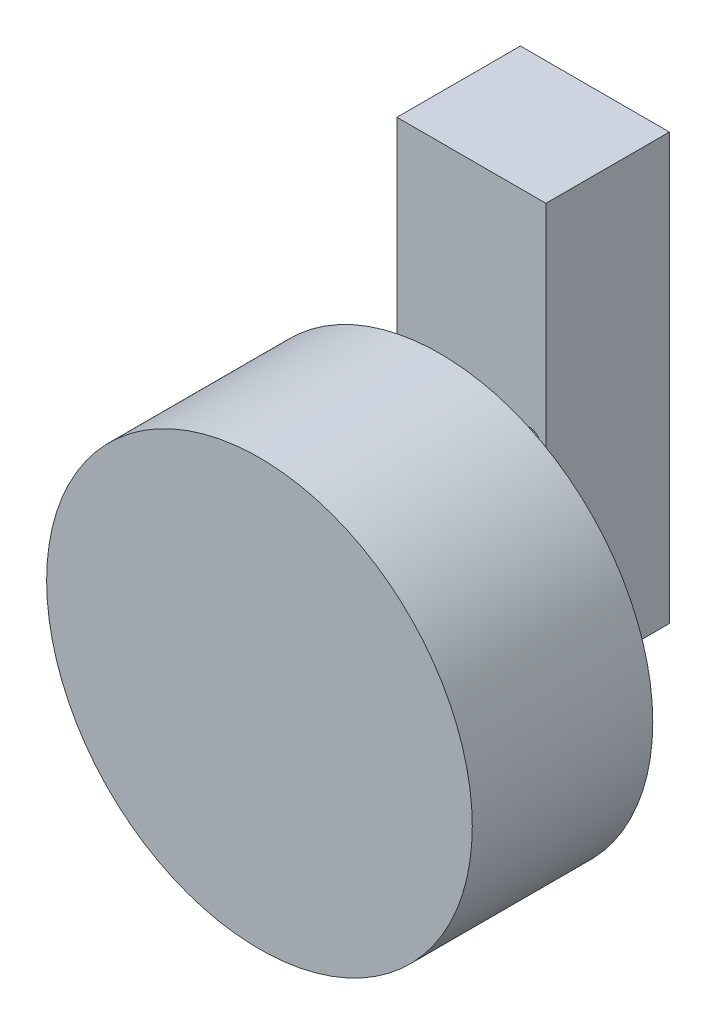
SolidWorks part; units mm, degrees
ref_plane "Front Plane" through (0, 0, 0) normal (0, 0, 1) x (1, 0, 0)
ref_plane "Top Plane" through (0, 0, 0) normal (0, 1, 0) x (1, 0, 0)
ref_plane "Right Plane" through (0, 0, 0) normal (1, 0, 0) x (0, 0, -1)
sketch "Sketch1" plane through (0, 0, 0) normal (0, 0, 1) x (1, 0, 0)
  line L1 (-32.7816, 32.4377) -> (-10.5566, 32.4377)
  line L2 (-32.7816, 32.4377) -> (-32.7816, -31.0623)
  line L3 (-32.7816, -31.0623) -> (-10.5566, -31.0623)
  line L4 (-10.5566, 32.4377) -> (-10.5566, -31.0623)
  circle A0 centre (-30.3686, 0.6877) radius 1.5875
  circle A1 centre (-12.9696, 0.6877) radius 1.5875
  point P8 (0, 0)
  dimension "D3" = 3.175
  dimension "D4" = 3.175
  dimension "D1" = 63.5
  dimension "D2" = 22.225
  dimension "D5" = 17.399
  dimension "D6" = 2.413
  dimension "D7" = 31.75
extrude "Boss-Extrude1" add sketch "Sketch1" along normal blind 18.415
sketch "Sketch2" plane through (0, 0, 18.415) normal (0, 0, 1) x (1, 0, 0)
  line L0 (-10.5566, -31.0623) -> (-10.5566, 32.4377) construction
  line L1 (-32.7816, -31.0623) -> (-10.5566, -31.0623) construction
  circle A0 centre (-21.6691, -21.9183) radius 6.985
  point P0 (-21.6691, -21.9183)
  dimension "D3" = 13.97
  dimension "D1" = 11.1125
  dimension "D2" = 9.144
extrude "Boss-Extrude2" add sketch "Sketch2" along normal blind 4.699
sketch "Sketch3" plane through (0, 0, 23.114) normal (0, 0, 1) x (1, 0, 0)
  circle A0 centre (-21.6691, -21.9183) radius 31.75
  point P0 (-21.6691, -21.9183)
  dimension "D1" = 63.5
extrude "Boss-Extrude3" add sketch "Sketch3" along normal blind 26.924
